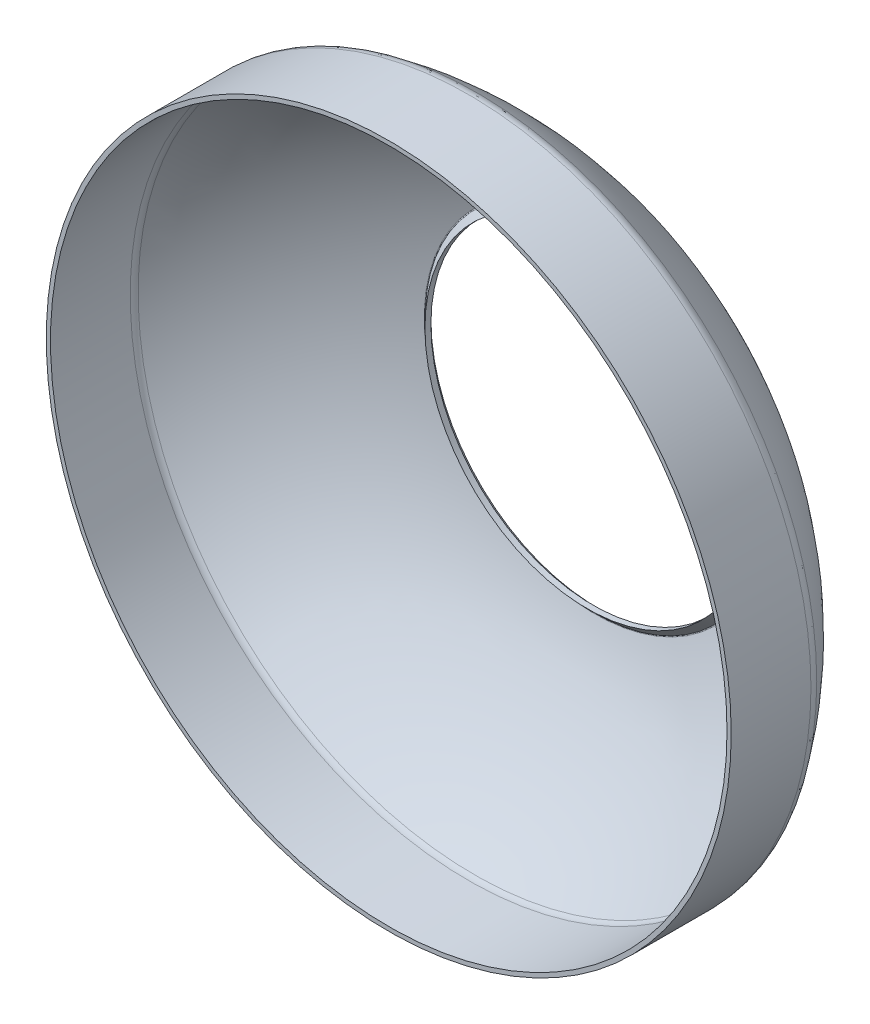
SolidWorks part; units mm, degrees
ref_plane "Přední rovina" through (0, 0, 0) normal (0, 0, 1) x (1, 0, 0)
ref_plane "Horní rovina" through (0, 0, 0) normal (0, 1, 0) x (1, 0, 0)
ref_plane "Pravá rovina" through (0, 0, 0) normal (1, 0, 0) x (0, 0, -1)
sketch "Skica1" plane through (0, 0, 0) normal (0, 1, 0) x (1, 0, 0)
  line L0 (-32.5, 0) -> (-32.5, 7.5651)
  line L1 (-32.5, 0) -> (0, 0) construction
  line L2 (0, 0) -> (0, 23.8456) construction
  line L3 (-15.7899, 19.7899) -> (-15.4, 19.4)
  line L4 (-15.4, 19.4) -> (-15.4, 18.8343)
  line L6 (-32.1, 0) -> (-32.1, 7.5651)
  line L7 (-16.0728, 19.5071) -> (-15.4, 18.8343)
  line L8 (-16.0728, 19.5071) -> (-15.5657, 19) construction
  line L9 (-15.5657, 19) -> (-13.294, 19) construction
  line L10 (-32.5, 0) -> (-12.3, 19.4) construction
  line L11 (-32.1, 0.9388) -> (-13.294, 19) construction
  line L12 (-32.5, 0) -> (-32.1, 0)
  line L13 (-32.1, 0.9388) -> (-32.1, 7.5651) construction
  line L14 (-15.4, 19.4) -> (-12.3, 19.4) construction
  arc A0 (-32.2476, 8.367) -> (-16.2873, 19.9152) centre (-7.6563, -8.8164) cw
  arc A1 (-32.5, 7.5651) -> (-32.2476, 8.367) centre (-31.1, 7.5651) cw
  arc A2 (-16.2873, 19.9152) -> (-15.7899, 19.7899) centre (-16.1435, 19.4364) cw
  arc A3 (-32.1, 7.5651) -> (-31.9197, 8.1379) centre (-31.1, 7.5651) cw
  arc A4 (-31.9197, 8.1379) -> (-16.1723, 19.5322) centre (-7.6563, -8.8164) cw
  arc A5 (-16.1723, 19.5322) -> (-16.0728, 19.5071) centre (-16.1435, 19.4364) cw
  point P9 (-32.5, 8)
  point P17 (-16, 20)
  dimension "D5" = 30
  dimension "D6" = 1.4
  dimension "D10" = 0.5
  dimension "D1" = 8
  dimension "D2" = 32.5
  dimension "D3" = 20
  dimension "D4" = 16
  dimension "D7" = 45
  dimension "D8" = 15.4
  dimension "D11" = 0.4
revolve "Rotovat1" add sketch "Skica1" angle 360 about L2
ref_plane "Rovina1" through (0, 0, -19.4) normal (0, 0, 1) x (1, 0, 0)
sketch "Skica2" plane through (0, 0, -19.4) normal (0, 0, 1) x (1, 0, 0)
  circle A0 centre (0, 0) radius 12.35
  dimension "D1" = 24.7
curve "Šroubovice/spirála1" pitch 1.8 height 1.8 turns 1
equation "\"PPlocha [mm2] - > [dm2]\"= \"Plocha\" / 10000"
